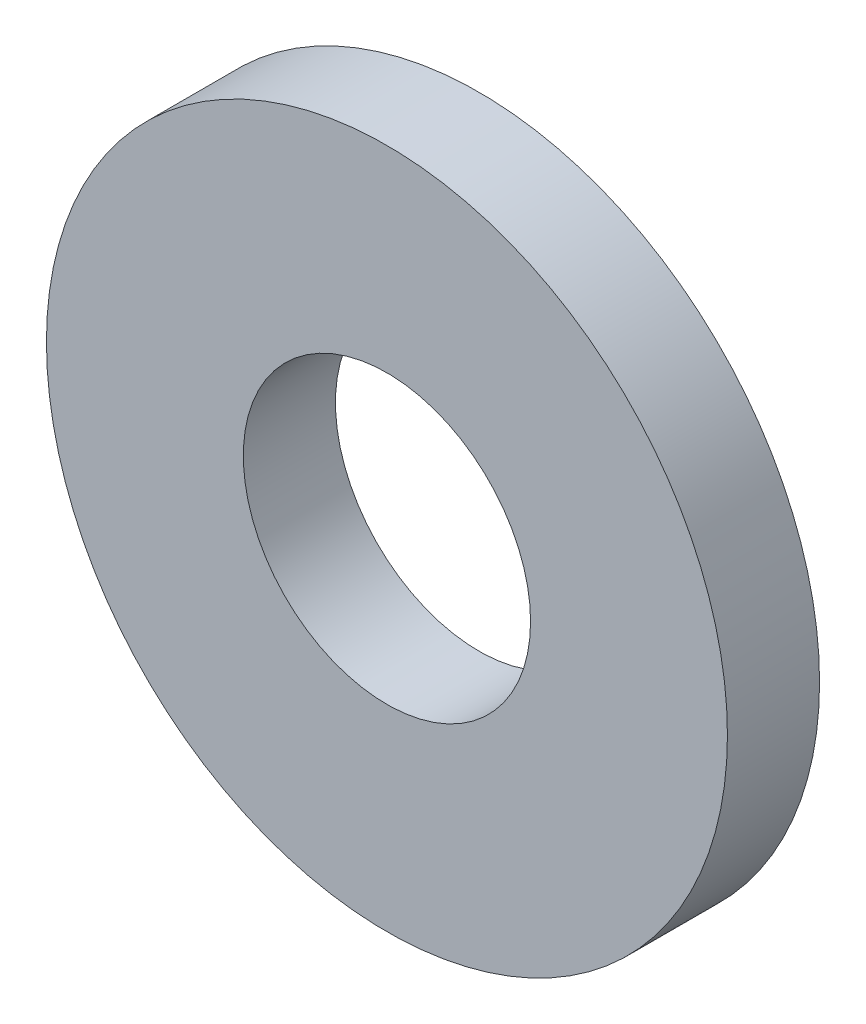
SolidWorks part; units mm, degrees
material "Silicon Rubber"
ref_plane "Front Plane" through (0, 0, 0) normal (0, 0, 1) x (1, 0, 0)
ref_plane "Top Plane" through (0, 0, 0) normal (0, 1, 0) x (1, 0, 0)
ref_plane "Right Plane" through (0, 0, 0) normal (1, 0, 0) x (0, 0, -1)
sketch "Sketch1" plane through (0, 0, 0) normal (0, 0, 1) x (1, 0, 0)
  circle A0 centre (0, 0) radius 3.683
  circle A1 centre (0, 0) radius 8.7312
  dimension "ID" = 7.366
  dimension "OD" = 17.4625
extrude "Extrude1" add sketch "Sketch1" against normal blind 2.3622
